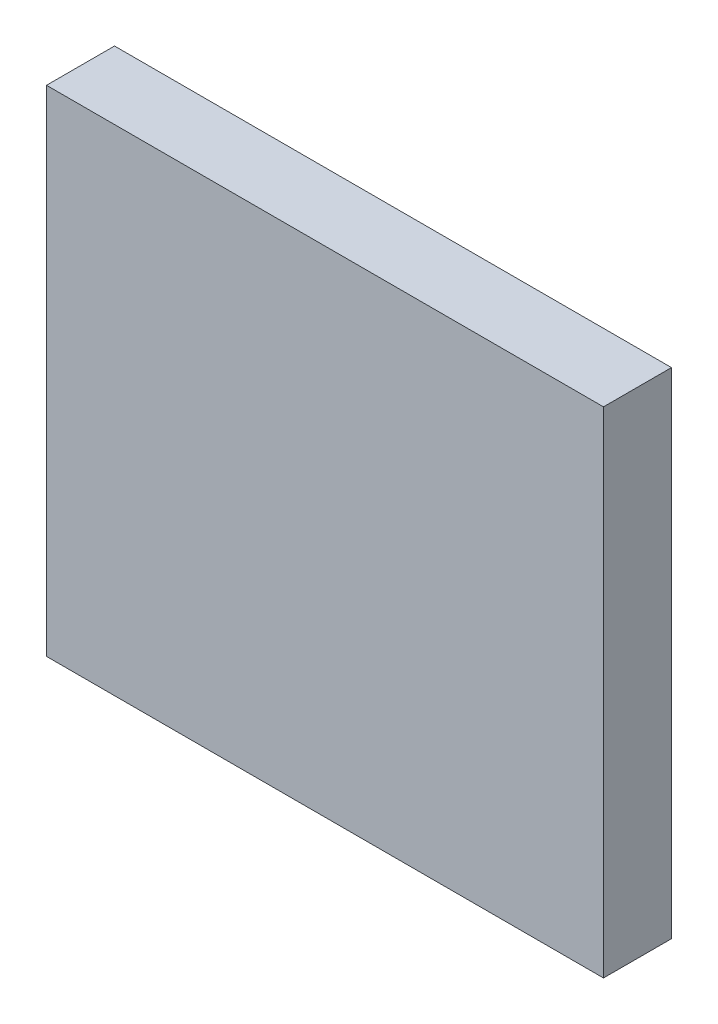
SolidWorks part; units mm, degrees
ref_plane "Front Plane" through (0, 0, 0) normal (0, 0, 1) x (1, 0, 0)
ref_plane "Top Plane" through (0, 0, 0) normal (0, 1, 0) x (1, 0, 0)
ref_plane "Right Plane" through (0, 0, 0) normal (1, 0, 0) x (0, 0, -1)
sketch "Sketch1" plane through (0, 0, 0) normal (0, 0, 1) x (1, 0, 0)
  line L0 (-35.1844, 29.1232) -> (-35.1844, -43.6109)
  line L1 (-35.1844, -43.6109) -> (46.7154, -43.6109)
  line L2 (46.7154, -43.6109) -> (46.7154, 29.1232)
  line L3 (46.7154, 29.1232) -> (-35.1844, 29.1232)
extrude "Boss-Extrude1" add sketch "Sketch1" along normal blind 10 contours L3 L0 L1 L2
